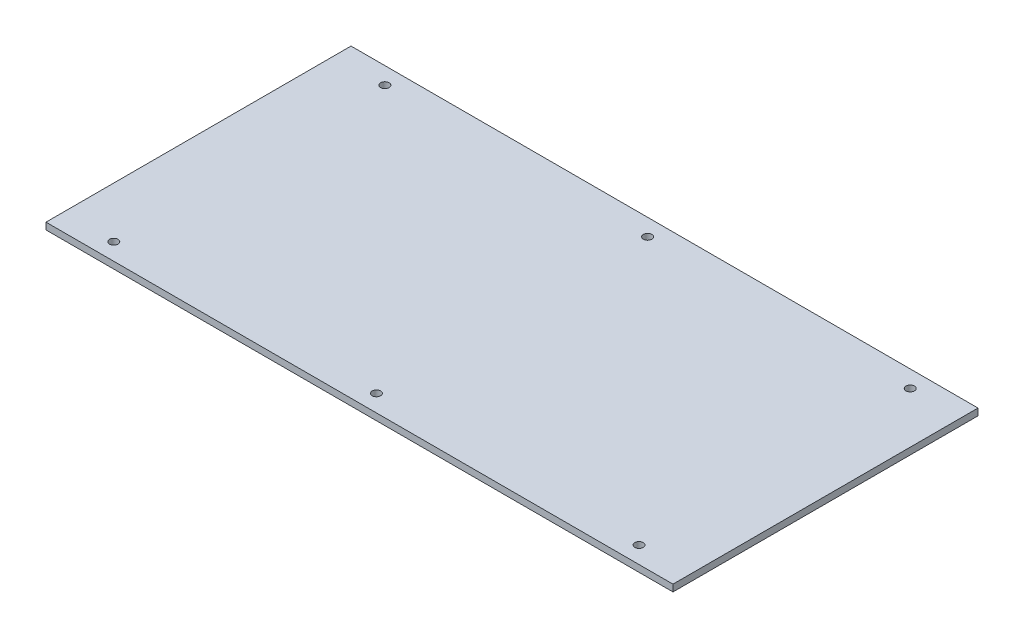
SolidWorks part; units mm, degrees
ref_plane "Front Plane" through (0, 0, 0) normal (0, 0, 1) x (1, 0, 0)
ref_plane "Top Plane" through (0, 0, 0) normal (0, 1, 0) x (1, 0, 0)
ref_plane "Right Plane" through (0, 0, 0) normal (1, 0, 0) x (0, 0, -1)
sketch "Sketch1" plane through (0, 0, 0) normal (0, 1, 0) x (1, 0, 0)
  line L0 (0, 90) -> (0, -90) construction
  line L1 (-185, -90) -> (185, -90)
  line L2 (-185, -90) -> (-185, 90)
  line L3 (-185, 90) -> (185, 90)
  line L4 (185, -90) -> (185, 90)
  line L5 (-185, -90) -> (185, 90) construction
  line L6 (-185, 90) -> (185, -90) construction
  line L7 (-185, 0) -> (185, 0) construction
  circle A0 centre (-155, 80) radius 2.5
  circle A1 centre (0, 80) radius 2.5
  circle A2 centre (155, 80) radius 2.5
  circle A3 centre (-155, -80) radius 2.5
  circle A4 centre (0, -80) radius 2.5
  circle A5 centre (155, -80) radius 2.5
  point P0 (0, 0)
  dimension "D3" = 5
  dimension "D4" = 5
  dimension "D7" = 30
  dimension "D1" = 180
  dimension "D2" = 370
  dimension "D5" = 10
  dimension "D6" = 10
extrude "Boss-Extrude1" add sketch "Sketch1" along normal blind 4
